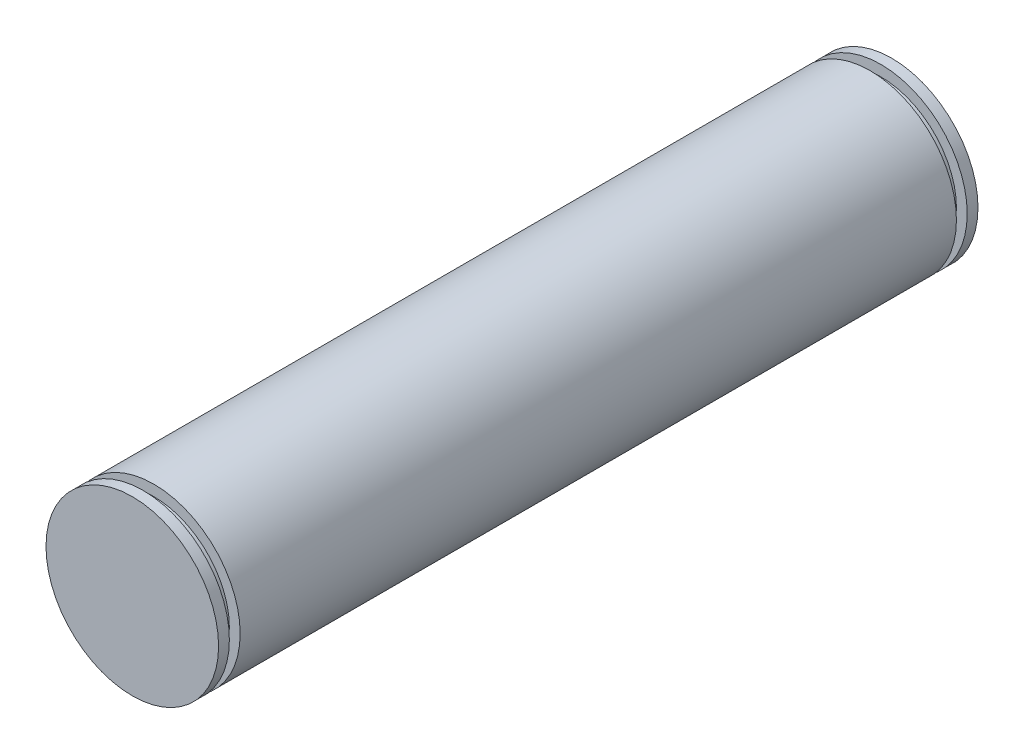
SolidWorks part; units mm, degrees
ref_plane "Front Plane" through (0, 0, 0) normal (0, 0, 1) x (1, 0, 0)
ref_plane "Top Plane" through (0, 0, 0) normal (0, 1, 0) x (1, 0, 0)
ref_plane "Right Plane" through (0, 0, 0) normal (1, 0, 0) x (0, 0, -1)
sketch "Sketch1" plane through (0, 0, 0) normal (0, 1, 0) x (1, 0, 0)
  line L0 (0, 0) -> (0.0981, 55.88) construction
  line L1 (0, 0) -> (12.7, 0)
  line L2 (12.7, 0) -> (12.7, 1.5875)
  line L3 (12.7, 1.5875) -> (11.1125, 1.5875)
  line L4 (11.1125, 1.5875) -> (11.1125, 3.175)
  line L5 (11.1125, 3.175) -> (12.7, 3.175)
  line L6 (12.7, 3.175) -> (12.7, 108.585)
  line L7 (0.0981, 55.88) -> (12.7, 55.88) construction
  line L8 (11.1125, 108.585) -> (12.7, 108.585)
  line L9 (11.1125, 110.1725) -> (11.1125, 108.585)
  line L10 (12.7, 110.1725) -> (11.1125, 110.1725)
  line L11 (12.7, 111.76) -> (12.7, 110.1725)
  line L12 (0, 111.76) -> (12.7, 111.76)
  line L13 (0, 0) -> (0, 111.76)
  dimension "D1" = 12.7
  dimension "D2" = 55.88
  dimension "D3" = 1.5875
  dimension "D4" = 1.5875
  dimension "D5" = 1.5875
revolve "Revolve1" add sketch "Sketch1" angle 360 about L13
